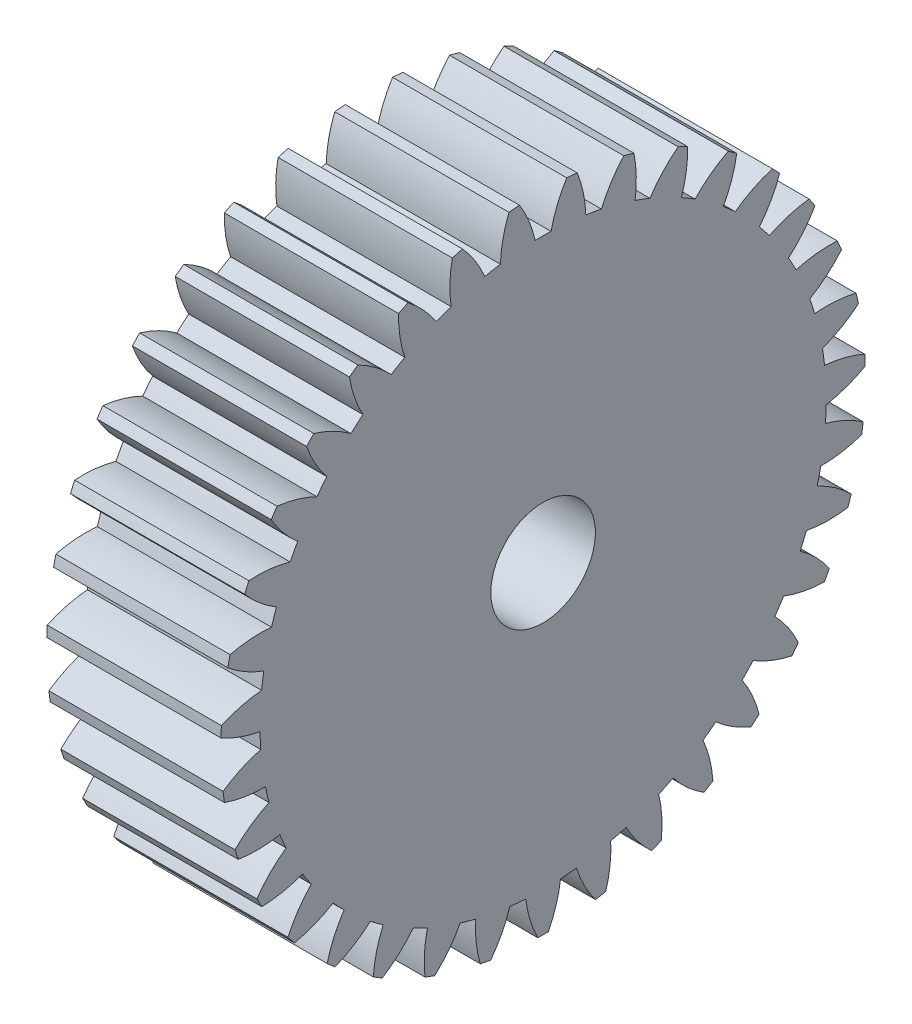
SolidWorks part; units mm, degrees
ref_plane "Plane1" through (0, 0, 0) normal (0, 0, 1) x (1, 0, 0)
ref_plane "Plane2" through (0, 0, 0) normal (0, 1, 0) x (1, 0, 0)
ref_plane "Plane3" through (0, 0, 0) normal (1, 0, 0) x (0, 0, -1)
other "Configuration Table"
sketch "HoldingSke" plane through (0, 0, 0) normal (0, 1, 0) x (1, 0, 0)
  line L0 (0, 0) -> (0.8192, -0.5736)
  line L1 (-15, 0) -> (100, 0) construction
  line L2 (0, 0) -> (-2.1039, 2.3779)
  line L3 (0, 0) -> (-11.863, 4.5341)
  line L4 (0, 0) -> (7.0742, 4.9534)
  line L5 (0, 0) -> (-46.8476, -17.4728)
  line L6 (0, 0) -> (-8.2896, -5.593)
  line L7 (-2.1039, 2.3779) -> (8.6586, 51.2059)
  line L8 (-76.2, 54.61) -> (-75.2, 54.61)
  line L9 (-71.009, 38.7566) -> (-53.1078, 45.2721)
  line L10 (-76.2, 71.12) -> (104.1128, 71.12)
  line L11 (0, 0) -> (-10, 0)
  line L12 (-76.2, 101.6) -> (-76.162, 101.6)
  line L13 (24.9733, 27.94) -> (52.9518, 28.4284)
  line L14 (24.9733, 27.94) -> (24.9743, 27.94)
  line L15 (24.9733, 27.94) -> (100.4006, 29.5858)
  line L16 (-63.627, -1) -> (-12.827, -1)
  circle A0 centre (0, 0) radius 3
  circle A1 centre (0, 0) radius 16.249
  circle A2 centre (0, 0) radius 37.5
  circle A3 centre (0, 0) radius 3
  dimension "MHD" = 32.498
  dimension "Hub_dia" = 75
  dimension "Bore" = 6
  dimension "MBD" = 6
  dimension "Num_teeth" = 35
  dimension "Pitch" = 1
  dimension "Overall_len" = 50
  dimension "Show_teeth" = 35
  dimension "Thickness" = 10
  dimension "OAL" = 50.0001
  dimension "T_dim" = 1
  dimension "Ap" = 20
  dimension "H" = 19.05
  dimension "Pitch_radius" = 180.3128
  dimension "Width" = 10
  dimension "Backlash" = 0.038
  dimension "Addendum_fac" = 1
  dimension "Dedendum_fac" = 1.25
  dimension "Clearance_fac" = 0.25
  dimension "Dedendum_add" = 0.001
  dimension "Module" = 1
sketch "BasProSke" plane through (0, 0, 0) normal (0, 1, 0) x (1, 0, 0)
  line L0 (-10, 0) -> (60, 0) construction
  line L1 (0, 0) -> (0, 18.5)
  line L2 (0, 0) -> (10, 0)
  line L3 (10, 0) -> (10, 18.5)
  line L4 (10, 18.5) -> (0, 18.5)
  dimension "Thickness" = 10
  dimension "Diameter" = 37
revolve "Base-Revolve" add sketch "BasProSke" angle 360 about L0
sketch "TooCutSke" plane through (0, 0, 0) normal (1, 0, 0) x (0, 0, -1)
  line L1 (0, 0) -> (0, 107) construction
  line L2 (0, 0) -> (-0.8516, 17.4793) construction
  line L3 (0, 0) -> (-3.1347, 34.8297) construction
  line L4 (-0.8516, 17.4793) -> (-1.5674, 17.4148) construction
  arc A0 (0.4564, 16.2426) -> (-0.4564, 16.2426) centre (0, 0) ccw
  arc A1 (1.373, 18.4745) -> (-1.373, 18.4745) centre (0, 0) ccw
  circle A2 centre (0, 0) radius 17.5 construction
  circle A3 centre (0, 0) radius 16.4446 construction
  arc A4 (-0.4564, 16.2426) -> (-1.373, 18.4745) centre (-7.293, 14.739) ccw
  arc A5 (1.373, 18.4745) -> (0.4564, 16.2426) centre (7.293, 14.739) ccw
  dimension "Root_dia" = 32.498
  dimension "Overcut_dia" = 37.0508
  dimension "Pitch_dia" = 35
  dimension "Base_dia" = 32.8892
  dimension "Flank_rad" = 7
  dimension "Half_ang" = 5.143
  dimension "Half_CT" = 0.7186
extrude "ToothCut" cut sketch "TooCutSke" along normal through all
fillet "Breaks" [suppressed] radius 0.02
fillet "RootFillets" [suppressed] radius 0.251
pattern_circular "TeethCuts" count 35 every 10.286 about axis through (-10, 0, 0) along (1, 0, 0) of "ToothCut", "RootFillets", "Breaks"
sketch "HubNeaOneSke" plane through (0, 0, 0) normal (-1, 0, 0) x (0, 0, 1)
  circle A0 centre (0, 0) radius 16.249
  dimension "Diameter" = 32.498
extrude "HubNearOne" [suppressed] add sketch "HubNeaOneSke" along normal blind 40.0001
sketch "HubNeaBotSke" plane through (0, 0, 0) normal (-1, 0, 0) x (0, 0, 1)
  circle A0 centre (0, 0) radius 16.249
  dimension "Diameter" = 32.498
extrude "HubNearBoth" [suppressed] add sketch "HubNeaBotSke" along normal blind 20
ref_plane "FarPln" through (10, 0, 0) normal (1, 0, 0) x (0, 0, -1)
sketch "HubFarSke" plane through (10, 0, 0) normal (1, 0, 0) x (0, 0, -1)
  circle A0 centre (0, 0) radius 16.249
  dimension "Diameter" = 32.498
extrude "HubFar" [suppressed] add sketch "HubFarSke" along normal blind 20
sketch "BorSke" plane through (0, 0, 0) normal (1, 0, 0) x (0, 0, -1)
  circle A0 centre (0, 0) radius 3
  dimension "Diameter" = 6
extrude "Bore" cut sketch "BorSke" along normal mid plane 100.0001
sketch "KeySke" plane through (0, 0, 0) normal (1, 0, 0) x (0, 0, -1)
  line L0 (-1, 0) -> (-1, 4)
  line L1 (-1, 4) -> (1, 4)
  line L2 (1, 4) -> (1, 0)
  line L3 (0, 0) -> (0, 34) construction
  line L4 (-1, 0) -> (1, 0)
  dimension "Offset" = 4
  dimension "Width" = 2
extrude "Keyway" [suppressed] cut sketch "KeySke" along normal mid plane 100.0001
pattern_circular "Keyway2" [suppressed] count 2 every 90 about axis through (-10, 0, 0) along (1, 0, 0)
equation "' \"Module@HoldingSke\" = 6.35"
equation "' \"Num_teeth@HoldingSke\" = 12"
equation "' \"Ap@HoldingSke\" =  20"
equation "' \"Ap@HoldingSke\" = 20"
equation "' \"Width@HoldingSke\" = 0.5 * 25.4"
equation "' \"Hub_dia@HoldingSke\"= 1 * 25.4"
equation "' \"Hub_dia@HoldingSke\" = 1 * 25.4"
equation "' \"Overall_len@HoldingSke\" = 1.0 * 25.4"
equation "' \"Bore@HoldingSke\" = 0.75 * 25.4"
equation "' \"T_dim@HoldingSke\" = 0.1 * 25.4"
equation "' \"Width@KeySke\" = 0.25 * 25.4"
equation "' \"Show_teeth@HoldingSke\" = 13"
equation "' \"Backlash@HoldingSke\" = 0.009 * 25.4"
equation "' \"Addendum_fac@HoldingSke\" = 1.0"
equation "' \"Dedendum_fac@HoldingSke\" = 1.25"
equation "' \"Dedendum_add@HoldingSke\" = 0.00005 * 25.4"
equation "' \"Clearance_fac@HoldingSke\" = 0.25"
equation "\"Pitch@HoldingSke\" = 1 / \"Module@HoldingSke\""
equation "\"Overcut_dia@TooCutSke\" = (\"Num_teeth@HoldingSke\" + 2 * \"Addendum_fac@HoldingSke\") / \"Pitch@HoldingSke\" + 0.002 * 25.4"
equation "\"Pitch_dia@TooCutSke\" = \"Num_teeth@HoldingSke\" / \"Pitch@HoldingSke\""
equation "\"Base_dia@TooCutSke\" = \"Num_teeth@HoldingSke\" / \"Pitch@HoldingSke\" * cos((\"Ap@HoldingSke\"  * 3.14159265 / 180))"
equation "\"Root_dia@TooCutSke\" = (\"Num_teeth@HoldingSke\" + 2) / \"Pitch@HoldingSke\" - 2 * (\"Addendum_fac@HoldingSke\" + \"Dedendum_fac@HoldingSke\") / \"Pitch@HoldingSke\" - \"Dedendum_add@HoldingSke\" * 2"
equation "\"Half_ang@TooCutSke\" = 180 / \"Num_teeth@HoldingSke\""
equation "\"Half_CT@TooCutSke\" = \"Num_teeth@HoldingSke\" / \"Pitch@HoldingSke\" * sin((3.14159265 / 2 / \"Num_teeth@HoldingSke\")) / 2 - 7 * \"Backlash@HoldingSke\" / 4"
equation "\"Flank_rad@TooCutSke\" = \"Num_teeth@HoldingSke\" / \"Pitch@HoldingSke\" / 5"
equation "\"Radius@RootFillets\" = \"Clearance_fac@HoldingSke\" / \"Pitch@HoldingSke\" + \"Dedendum_add@HoldingSke\""
equation "\"Break_rad@Breaks\" = 0.02 / \"Pitch@HoldingSke\""
equation "\"Thickness@HoldingSke\" = \"Width@HoldingSke\""
equation "\"OAL@HoldingSke\" = \"Thickness@HoldingSke\""
equation "\"MHD@HoldingSke\" = (\"Num_teeth@HoldingSke\" + 2) / \"Pitch@HoldingSke\" - 2 * (\"Addendum_fac@HoldingSke\" + \"Dedendum_fac@HoldingSke\")  / \"Pitch@HoldingSke\" - \"Dedendum_add@HoldingSke\" * 2"
equation "\"MBD@HoldingSke\" = (\"Num_teeth@HoldingSke\" + 2) / \"Pitch@HoldingSke\" - 2 * (\"Addendum_fac@HoldingSke\" + \"Dedendum_fac@HoldingSke\")  / \"Pitch@HoldingSke\" - \"Dedendum_add@HoldingSke\" * 2 - 0.002 * 25.4"
equation "\"MHD@HoldingSke\" = ((sgn( \"MHD@HoldingSke\" - \"Hub_dia@HoldingSke\" )-1)*( \"MHD@HoldingSke\" - \"Hub_dia@HoldingSke\" ))/-2+ \"Hub_dia@HoldingSke\""
equation "\"MBD@HoldingSke\" = ((sgn( \"MBD@HoldingSke\" - \"Bore@HoldingSke\" )-1)*( \"MBD@HoldingSke\" - \"Bore@HoldingSke\" ))/-2+ \"Bore@HoldingSke\""
equation "\"OAL@HoldingSke\" = ((sgn( \"OAL@HoldingSke\" - \"Overall_len@HoldingSke\" )+1)*( \"OAL@HoldingSke\" - \"Overall_len@HoldingSke\" ))/2 + \"Overall_len@HoldingSke\" + 0.000002 * 25.4"
equation "\"Num_teeth@TeethCuts\" = int( \"Show_teeth@HoldingSke\" ) + 1"
equation "\"Num_teeth@TeethCuts\" = ((sgn( \"Num_teeth@TeethCuts\" - \"Num_teeth@HoldingSke\" )-1)*( \"Num_teeth@TeethCuts\" - \"Num_teeth@HoldingSke\" ))/-2+ \"Num_teeth@HoldingSke\""
equation "\"Num_teeth@TeethCuts\" = ((sgn( \"Num_teeth@TeethCuts\" - 2.0)+1)*( \"Num_teeth@TeethCuts\" - 2.0))/2 +2.0"
equation "\"Angle@TeethCuts\" = 360.0 / \"Num_teeth@HoldingSke\""
equation "\"Diameter@BasProSke\" = (\"Num_teeth@HoldingSke\" + 2 * \"Addendum_fac@HoldingSke\") / \"Pitch@HoldingSke\""
equation "\"Thickness@BasProSke\"  = \"Thickness@HoldingSke\""
equation "' \"Fillet_rad@BasProSke\" =  \"Thickness@HoldingSke\" * 0.05"
equation "' \"Fillet_rad@BasProSke\" = \"Thickness@HoldingSke\" * 0.05"
equation "\"MHD@HoldingSke\" = ((sgn( \"MHD@HoldingSke\" - \"Root_dia@TooCutSke\" )-1)*( \"MHD@HoldingSke\" - \"Root_dia@TooCutSke\" ))/-2+ \"Root_dia@TooCutSke\""
equation "\"Diameter@HubNeaOneSke\" = \"MHD@HoldingSke\""
equation "\"Length@HubNearOne\" = \"OAL@HoldingSke\" - \"Thickness@BasProSke\""
equation "\"Diameter@HubNeaBotSke\" = \"MHD@HoldingSke\""
equation "\"Length@HubNearBoth\" = ( \"OAL@HoldingSke\" - \"Thickness@BasProSke\" ) / 2.0"
equation "\"Thickness@FarPln\" = \"Thickness@BasProSke\""
equation "\"Diameter@HubFarSke\" = \"MHD@HoldingSke\""
equation "\"Length@HubFar\" = ( \"OAL@HoldingSke\" - \"Thickness@BasProSke\" ) / 2.0"
equation "\"Diameter@BorSke\" = \"MBD@HoldingSke\""
equation "\"D1@Bore\" = \"OAL@HoldingSke\" * 2.0"
equation "\"D1@Keyway\" = \"OAL@HoldingSke\" * 2.0"
equation "\"Offset@KeySke\" = \"T_dim@HoldingSke\" + \"MBD@HoldingSke\" / 2.0"
